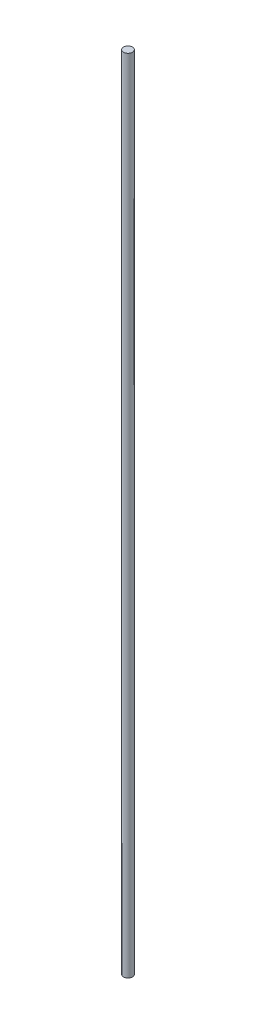
SolidWorks part; units mm, degrees
ref_plane "Front Plane" through (0, 0, 0) normal (0, 0, 1) x (1, 0, 0)
ref_plane "Top Plane" through (0, 0, 0) normal (0, 1, 0) x (1, 0, 0)
ref_plane "Right Plane" through (0, 0, 0) normal (1, 0, 0) x (0, 0, -1)
sketch "Sketch1" plane through (0, 0, 0) normal (0, 1, 0) x (1, 0, 0)
  circle A0 centre (0, 0) radius 19.05
  dimension "D1" = 38.1
extrude "Boss-Extrude1" add sketch "Sketch1" along normal blind 3403.6
